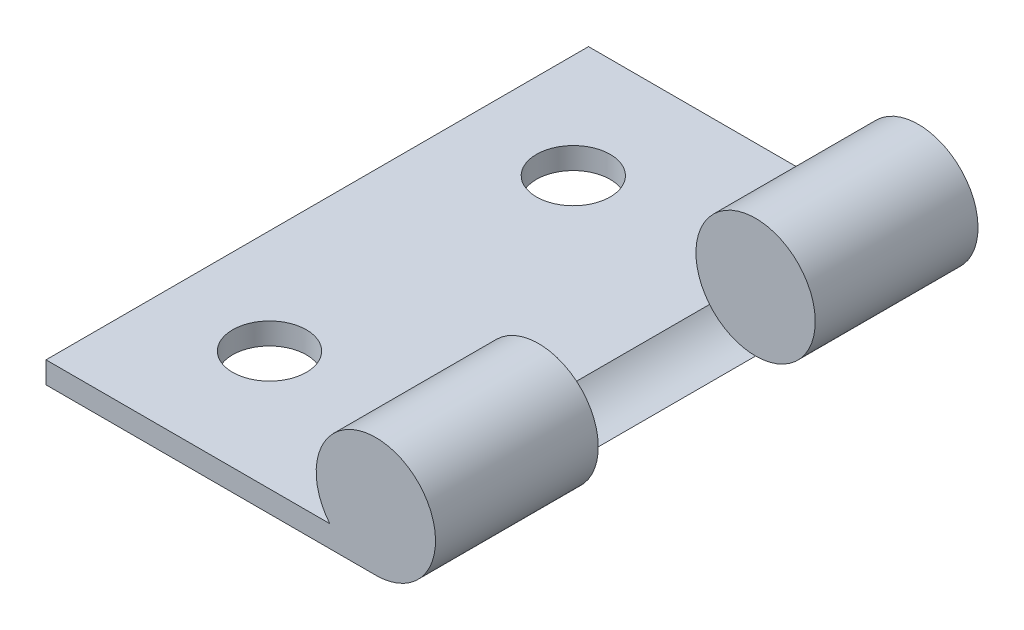
SolidWorks part; units mm, degrees
material "AISI 304"
ref_plane "前视基准面" through (0, 0, 0) normal (0, 0, 1) x (1, 0, 0)
ref_plane "上视基准面" through (0, 0, 0) normal (0, 1, 0) x (1, 0, 0)
ref_plane "右视基准面" through (0, 0, 0) normal (1, 0, 0) x (0, 0, -1)
sketch "草图1" plane through (0, 0, 0) normal (0, 0, 1) x (1, 0, 0)
  line L0 (0, 0) -> (-12.3968, 0) construction
  line L1 (0, 7.4382) -> (0, -11.9267) construction
  line L2 (0, -2.75) -> (-15.2, -2.75)
  line L3 (-15.2, -2.75) -> (-15.2, -1.75)
  line L4 (-15.2, -1.75) -> (-2.1213, -1.75)
  arc A0 (0, -2.75) -> (-2.1213, -1.75) centre (0, 0) ccw
  dimension "D2" = 5.5
  dimension "D1" = 1
  dimension "D3" = 15.2
extrude "凸台-拉伸1" add sketch "草图1" along normal blind 25
sketch "草图2" plane through (0, -1.75, 0) normal (0, 1, 0) x (1, 0, 0)
  line L0 (-15.2, -12.5) -> (7.5492, -12.5) construction
  line L1 (-15.2, -25) -> (-15.2, 0) construction
  circle A0 centre (-10.4, -5.5) radius 1.7
  circle A1 centre (-10.4, -19.5) radius 1.7
  dimension "D3" = 3.4
  dimension "D1" = 14
  dimension "D2" = 10.4
extrude "切除-拉伸1" cut sketch "草图2" against normal blind 25
sketch "草图3" plane through (0, 0, 0) normal (0, 0, -1) x (-1, 0, 0)
  circle A0 centre (0, 0) radius 2.75
extrude "切除-拉伸2" cut sketch "草图3" against normal blind 10 from offset 7.5
